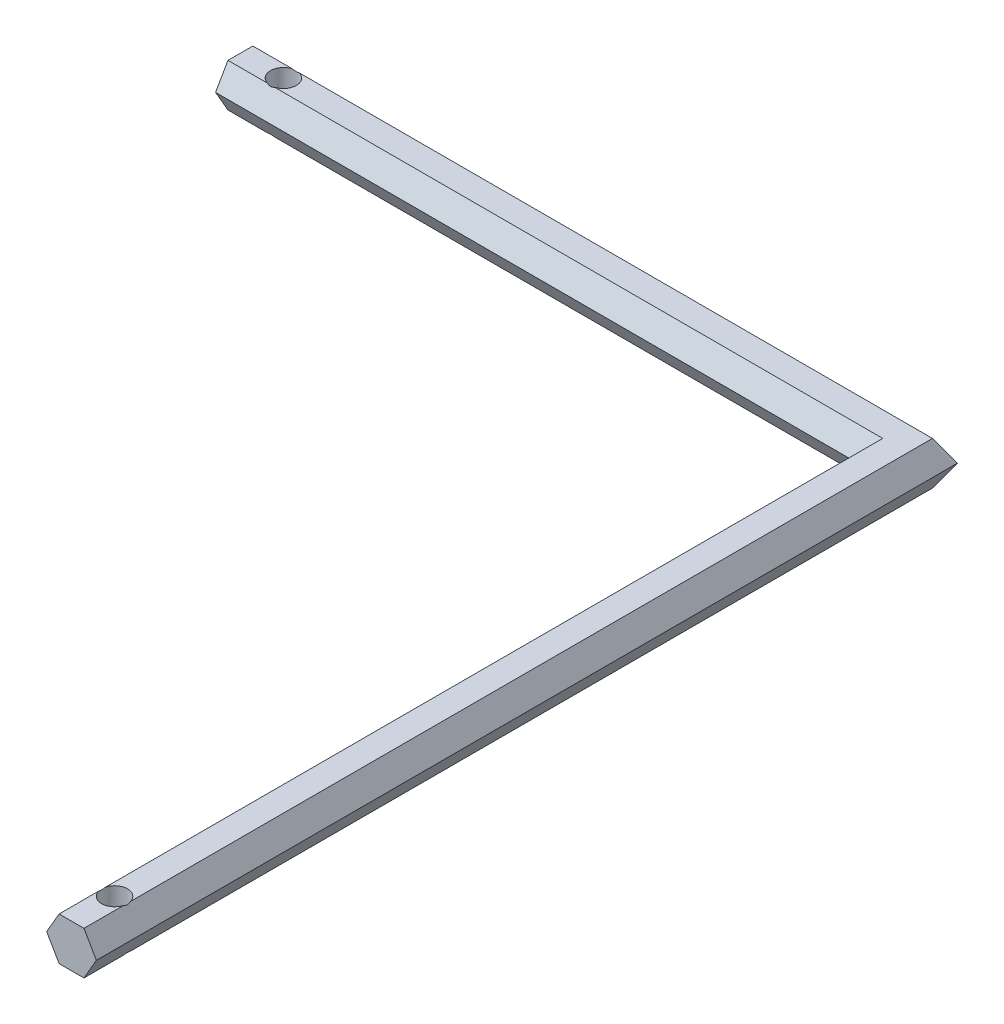
SolidWorks part; units mm, degrees
ref_plane "Plano frontal" through (0, 0, 0) normal (0, 0, 1) x (1, 0, 0)
ref_plane "Plano superior" through (0, 0, 0) normal (0, 1, 0) x (1, 0, 0)
ref_plane "Plano direito" through (0, 0, 0) normal (1, 0, 0) x (0, 0, -1)
sketch "Sketch1" plane through (0, 0, 0) normal (0, 0, 1) x (1, 0, 0)
  line L1 (-5.7735, 0) -> (-2.8868, -5)
  line L2 (-2.8868, -5) -> (2.8868, -5)
  line L3 (2.8868, -5) -> (5.7735, 0)
  line L4 (5.7735, 0) -> (2.8868, 5)
  line L5 (2.8868, 5) -> (-2.8868, 5)
  line L6 (-2.8868, 5) -> (-5.7735, 0)
  circle A0 centre (0, 0) radius 5 construction
  dimension "D1" = 10
extrude "Boss-Extrude1" add sketch "Sketch1" along normal mid plane 200
sketch "Sketch2" plane through (0, 0, 0) normal (0, 1, 0) x (1, 0, 0)
  line L0 (-35.287, 100) -> (36.1141, 100) construction
  line L1 (5.7735, 100) -> (-5.7735, 88.453)
  line L2 (-5.7735, -100) -> (-5.7735, 100) construction
  line L3 (-5.7735, 88.453) -> (-5.7735, 100)
  line L4 (-5.7735, 100) -> (5.7735, 100)
  dimension "D1" = 45
extrude "Cut-Extrude1" cut sketch "Sketch2" against normal through all both and the other way through all
ref_plane "Plane1" through (-155, 0, 0) normal (-1, 0, 0) x (0, 0, 1)
sketch "Sketch4" plane through (-155, 0, 0) normal (-1, 0, 0) x (0, 0, 1)
  line L0 (-91.3397, 5) -> (-97.1132, 5) construction
  line L1 (-97.1132, 5) -> (-100, 0)
  line L2 (-100, 0) -> (-97.1132, -5)
  line L3 (-97.1132, -5) -> (-91.3397, -5)
  line L4 (-91.3397, -5) -> (-88.453, 0)
  line L5 (-88.453, 0) -> (-91.3397, 5)
  line L6 (-91.3397, 5) -> (-97.1132, 5)
  line L7 (-91.3397, -5) -> (-97.1132, -5) construction
  line L8 (-88.453, 0) -> (-91.3397, -5) construction
  circle A0 centre (-94.2265, 0) radius 5 construction
  dimension "D1" = 10
  dimension "D2" = 10
  dimension "D3" = 10
loft "Loft1" add profiles "Sketch4" section "Sketch4" section face at (0, 0, -94.2265)
sketch "Sketch5" plane through (0, 0, 0) normal (0, 1, 0) x (1, 0, 0)
  line L3 (0, 136.5061) -> (0, -132.701) construction
  line L4 (-189.6969, 88.453) -> (-165.9396, 88.453) construction
  line L6 (-53.4124, 100) -> (-189.6969, 100) construction
  line L8 (-189.6969, 100) -> (-189.6969, 88.453) construction
  line L9 (-189.6969, 94.2265) -> (-126.1069, 94.2265) construction
  line L10 (2.8868, -100) -> (-2.8868, -100) construction
  line L11 (-155, 23.8493) -> (-155, -23.8493) construction
  circle A0 centre (0, -90) radius 3
  circle A1 centre (-145, 94.2265) radius 3
  point P7 (-121.5546, 100)
  dimension "D2" = 6
  dimension "D3" = 6
  dimension "D1" = 11.547
  dimension "D4" = 10
  dimension "D5" = 10
extrude "Cut-Extrude2" cut sketch "Sketch5" against normal through all both and the other way through all
